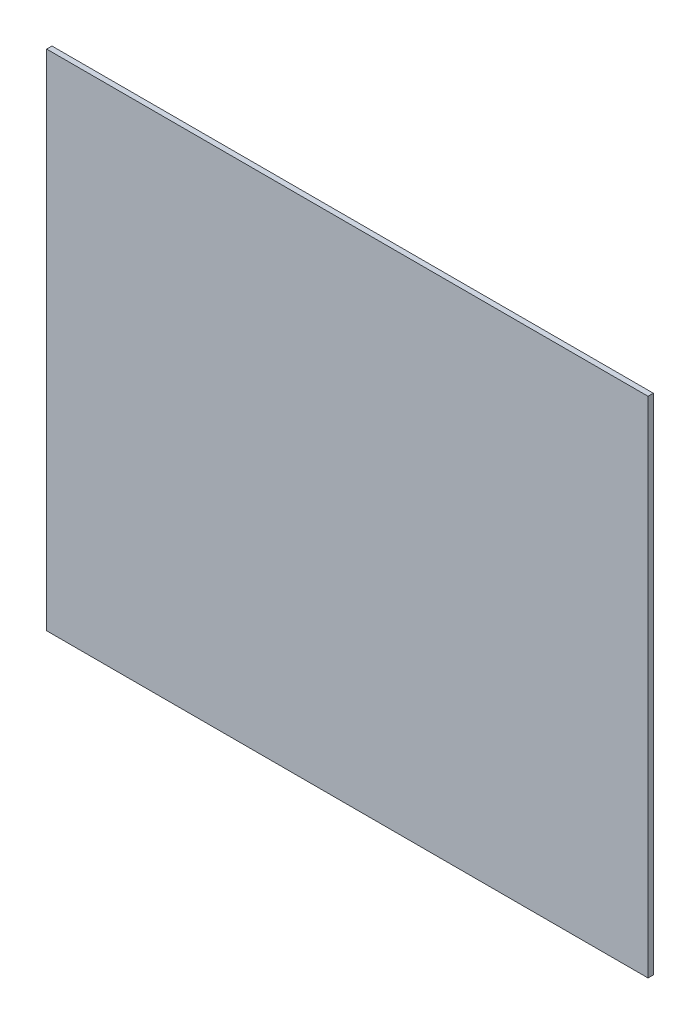
SolidWorks part; units mm, degrees
ref_plane "前视基准面" through (0, 0, 0) normal (0, 0, 1) x (1, 0, 0)
ref_plane "上视基准面" through (0, 0, 0) normal (0, 1, 0) x (1, 0, 0)
ref_plane "右视基准面" through (0, 0, 0) normal (1, 0, 0) x (0, 0, -1)
sketch "草图1" plane through (0, 0, 0) normal (0, 0, 1) x (1, 0, 0)
  line L0 (-85.0964, 56.1991) -> (253.9036, 56.1991)
  line L1 (253.9036, 56.1991) -> (253.9036, -227.8009)
  line L2 (253.9036, -227.8009) -> (-85.0964, -227.8009)
  line L3 (-85.0964, 56.1991) -> (-85.0964, -227.8009)
extrude "凸台-拉伸1" add sketch "草图1" along normal blind 3
